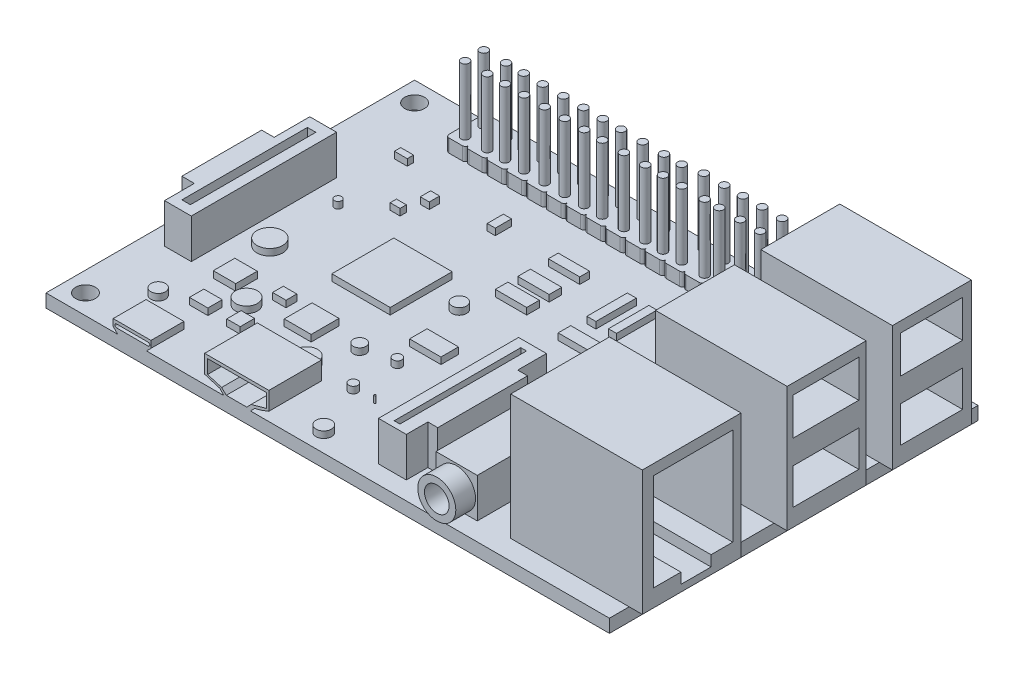
SolidWorks part; units mm, degrees
ref_plane "前视基准面" through (0, 0, 0) normal (0, 0, 1) x (1, 0, 0)
ref_plane "上视基准面" through (0, 0, 0) normal (0, 1, 0) x (1, 0, 0)
ref_plane "右视基准面" through (0, 0, 0) normal (1, 0, 0) x (0, 0, -1)
sketch "草图1" plane through (0, 0, 0) normal (0, 1, 0) x (1, 0, 0)
  line L1 (-42.8, -28) -> (42.8, -28)
  line L2 (-42.8, -28) -> (-42.8, 28)
  line L3 (-42.8, 28) -> (42.8, 28)
  line L4 (42.8, -28) -> (42.8, 28)
  line L5 (-42.8, -28) -> (42.8, 28) construction
  line L6 (-42.8, 28) -> (42.8, -28) construction
  circle A0 centre (-39.8, 25) radius 1.5
  circle A3 centre (-39.8, -25) radius 1.5
  point P0 (0, 0)
  dimension "D3" = 3
  dimension "D4" = 3
  dimension "D1" = 85.6
  dimension "D2" = 56
  dimension "D10" = 3
extrude "凸台-拉伸1" add sketch "草图1" along normal blind 2
sketch "草图2" plane through (0, 2, 0) normal (0, 1, 0) x (1, 0, 0)
  line L0 (42.8, -28) -> (42.8, 28) construction
  line L1 (24.8, -25) -> (44.8, -25)
  line L2 (24.8, -25) -> (24.8, -10)
  line L3 (24.8, -10) -> (44.8, -10)
  line L4 (44.8, -25) -> (44.8, -10)
  line L5 (24.8, -3) -> (44.8, -3)
  line L6 (24.8, -3) -> (24.8, 9)
  line L7 (24.8, 9) -> (44.8, 9)
  line L8 (44.8, -3) -> (44.8, 9)
  line L9 (24.8, 13) -> (44.8, 13)
  line L10 (24.8, 13) -> (24.8, 25)
  line L11 (24.8, 25) -> (44.8, 25)
  line L12 (44.8, 13) -> (44.8, 25)
  line L13 (-42.8, -28) -> (42.8, -28) construction
  line L14 (42.8, 28) -> (-42.8, 28) construction
  point P16 (34.8, 25)
  dimension "D1" = 12
  dimension "D2" = 12
  dimension "D3" = 15
  dimension "D4" = 20
  dimension "D5" = 2
  dimension "D6" = 2
  dimension "D7" = 20
  dimension "D8" = 20
  dimension "D9" = 2
  dimension "D10" = 3
  dimension "D11" = 3
  dimension "D12" = 4
extrude "凸台-拉伸2" add sketch "草图2" along normal blind 19
sketch "草图3" plane through (44.8, 0, 0) normal (1, 0, 0) x (0, 0, -1)
  line L0 (-23.3228, 19.3977) -> (-23.3228, 4.6356)
  line L1 (-23.3228, 4.6356) -> (-19.1436, 4.6356)
  line L2 (-19.1436, 4.6356) -> (-19.1436, 3.0178)
  line L3 (-19.1436, 3.0178) -> (-14.5599, 3.0178)
  line L4 (-14.5599, 3.0178) -> (-14.5599, 4.6356)
  line L5 (-14.5599, 4.6356) -> (-11.257, 4.6356)
  line L6 (-11.257, 4.6356) -> (-11.257, 19.3977)
  line L7 (-11.257, 19.3977) -> (-23.3228, 19.3977)
  line L9 (-2.0896, 19.3977) -> (7.8866, 19.3977)
  line L10 (-2.0896, 19.3977) -> (-2.0896, 13.7355)
  line L11 (-2.0896, 13.7355) -> (7.8866, 13.7355)
  line L12 (7.8866, 19.3977) -> (7.8866, 13.7355)
  line L13 (-2.0896, 10.0956) -> (7.8866, 10.0956)
  line L14 (-2.0896, 10.0956) -> (-2.0896, 4.6356)
  line L15 (-2.0896, 4.6356) -> (7.8866, 4.6356)
  line L16 (7.8866, 10.0956) -> (7.8866, 4.6356)
  line L17 (14.2229, 19.3977) -> (23.6598, 19.3977)
  line L18 (14.2229, 19.3977) -> (14.2229, 13.7355)
  line L19 (14.2229, 13.7355) -> (23.6598, 13.7355)
  line L20 (23.6598, 19.3977) -> (23.6598, 13.7355)
  line L21 (14.2229, 10.0956) -> (23.6598, 10.0956)
  line L22 (14.2229, 10.0956) -> (14.2229, 4.6356)
  line L23 (14.2229, 4.6356) -> (23.6598, 4.6356)
  line L24 (23.6598, 10.0956) -> (23.6598, 4.6356)
extrude "切除-拉伸1" cut sketch "草图3" against normal blind 18
sketch "草图4" plane through (0, 2, 0) normal (0, 1, 0) x (1, 0, 0)
  line L0 (4.9572, -25.2445) -> (4.9572, -3.9572)
  line L1 (13.6905, -25.2445) -> (19.9675, -25.2445)
  line L2 (13.6905, -25.2445) -> (13.6905, -10.2342)
  line L3 (13.6905, -10.2342) -> (19.9675, -10.2342)
  line L4 (19.9675, -25.2445) -> (19.9675, -10.2342)
  line L5 (4.9572, -3.9572) -> (9.1874, -3.9572)
  line L6 (9.1874, -3.9572) -> (9.1874, -8.3239)
  line L7 (9.1874, -8.3239) -> (10.6884, -8.3239)
  line L8 (10.6884, -8.3239) -> (10.6884, -21.9695)
  line L9 (10.6884, -21.9695) -> (9.1874, -21.9695)
  line L10 (9.1874, -21.9695) -> (9.1874, -25.2445)
  line L11 (9.1874, -25.2445) -> (4.9572, -25.2445)
  line L12 (-35.88, -12.8475) -> (-35.88, 9.2174)
  line L13 (6.4698, -24.3711) -> (7.3443, -24.3711)
  line L14 (6.4698, -24.3711) -> (6.4698, -5.1307)
  line L15 (6.4698, -5.1307) -> (7.3443, -5.1307)
  line L16 (7.3443, -24.3711) -> (7.3443, -5.1307)
  line L17 (-35.88, 9.2174) -> (-39.941, 9.2174)
  line L18 (-39.941, 9.2174) -> (-39.941, 3.8027)
  line L19 (-39.941, 3.8027) -> (-41.8361, 3.8027)
  line L20 (-41.8361, 3.8027) -> (-41.8361, -8.3239)
  line L21 (-41.8361, -8.3239) -> (-39.941, -8.3239)
  line L22 (-39.941, -8.3239) -> (-39.941, -12.8475)
  line L23 (-39.941, -12.8475) -> (-35.88, -12.8475)
  line L25 (-38.7205, -11.4317) -> (-37.4349, -11.4317)
  line L26 (-38.7205, -11.4317) -> (-38.7205, 7.6329)
  line L27 (-38.7205, 7.6329) -> (-37.4349, 7.6329)
  line L28 (-37.4349, -11.4317) -> (-37.4349, 7.6329)
extrude "凸台-拉伸3" add sketch "草图4" along normal blind 6
sketch "草图5" plane through (0, 0, 25.2445) normal (0, 0, 1) x (1, 0, 0)
  circle A0 centre (16.8166, 4.8134) radius 2.8909
  circle A1 centre (16.8166, 4.8134) radius 1.8682
extrude "凸台-拉伸4" add sketch "草图5" along normal blind 3
sketch "草图6" plane through (0, 0, 28) normal (0, 0, 1) x (1, 0, 0)
  line L0 (-31.9132, 2) -> (-32.596, 2.6828)
  line L1 (-42.8, 2) -> (16.1517, 2) construction
  line L2 (-32.596, 2.6828) -> (-32.596, 3.7273)
  line L3 (-32.596, 3.7273) -> (-26.8487, 3.7273)
  line L4 (-26.8487, 3.7273) -> (-26.8487, 2.6828)
  line L5 (-26.8487, 2.6828) -> (-27.5315, 2)
  line L6 (-27.5315, 2) -> (-31.9132, 2)
  line L7 (-32.093, 3.0167) -> (-27.2853, 3.0167) construction
  line L8 (-32.093, 3.2738) -> (-27.2853, 3.2738)
  line L9 (-32.093, 2.7595) -> (-27.2853, 2.7595)
  arc A0 (-32.093, 3.2738) -> (-32.093, 2.7595) centre (-32.093, 3.0167) ccw
  arc A1 (-27.2853, 2.7595) -> (-27.2853, 3.2738) centre (-27.2853, 3.0167) ccw
  point P10 (-29.6892, 3.0167)
extrude "凸台-拉伸5" add sketch "草图6" against normal blind 5
sketch "草图7" plane through (0, 0, 28) normal (0, 0, 1) x (1, 0, 0)
  line L0 (-18.6957, 6.1071) -> (-18.6957, 3.3548)
  line L1 (-18.6957, 3.3548) -> (-17.2094, 2.9048)
  line L2 (-17.2094, 2.9048) -> (-16.3918, 2.6574)
  line L3 (-16.3918, 2.6574) -> (-15.7754, 2)
  line L4 (-27.5315, 2) -> (16.1517, 2) construction
  line L5 (-15.7754, 2) -> (-11.7399, 2)
  line L6 (-11.7399, 2) -> (-11.0825, 2.6574)
  line L7 (-11.0825, 2.6574) -> (-10.1235, 2.9048)
  line L8 (-10.1235, 2.9048) -> (-8.9408, 3.3548)
  line L9 (-8.9408, 3.3548) -> (-8.9408, 6.1071)
  line L10 (-8.9408, 6.1071) -> (-18.6957, 6.1071)
  line L11 (-18.2447, 5.6338) -> (-18.2447, 3.5444)
  line L12 (-18.2447, 3.5444) -> (-16.1159, 2.9048)
  line L13 (-16.1159, 2.9048) -> (-15.4063, 2.2237)
  line L14 (-15.4063, 2.2237) -> (-12.2918, 2.2237)
  line L15 (-12.2918, 2.2237) -> (-11.638, 2.9048)
  line L16 (-11.638, 2.9048) -> (-9.3153, 3.5444)
  line L17 (-9.3153, 3.5444) -> (-9.3153, 5.6338)
  line L18 (-9.3153, 5.6338) -> (-18.2447, 5.6338)
extrude "凸台-拉伸6" add sketch "草图7" against normal blind 8
sketch "草图8" plane through (0, 2, 0) normal (0, 1, 0) x (1, 0, 0)
  line L0 (-24.5582, 21) -> (-22.5582, 21)
  line L1 (-30.5582, 21) -> (-28.5582, 21)
  line L2 (-31.0582, 21.5) -> (-31.0582, 23.5)
  line L3 (-30.5582, 24) -> (-28.5582, 24)
  line L4 (-28.0582, 21.5) -> (-28.0582, 23.5)
  line L5 (-30.5582, 24) -> (-28.5582, 24)
  line L6 (-31.0582, 24.5) -> (-31.0582, 26.5)
  line L7 (-30.5582, 27) -> (-28.5582, 27)
  line L8 (-28.0582, 24.5) -> (-28.0582, 26.5)
  line L9 (-25.0582, 21.5) -> (-25.0582, 23.5)
  line L10 (-24.5582, 24) -> (-22.5582, 24)
  line L11 (-22.0582, 21.5) -> (-22.0582, 23.5)
  line L12 (-24.5582, 24) -> (-22.5582, 24)
  line L13 (-25.0582, 24.5) -> (-25.0582, 26.5)
  line L14 (-24.5582, 27) -> (-22.5582, 27)
  line L15 (-22.0582, 24.5) -> (-22.0582, 26.5)
  line L16 (-27.5582, 21) -> (-25.5582, 21)
  line L17 (-28.0582, 21.5) -> (-28.0582, 23.5)
  line L18 (-27.5582, 24) -> (-25.5582, 24)
  line L19 (-25.0582, 21.5) -> (-25.0582, 23.5)
  line L20 (-27.5582, 24) -> (-25.5582, 24)
  line L21 (-28.0582, 24.5) -> (-28.0582, 26.5)
  line L22 (-27.5582, 27) -> (-25.5582, 27)
  line L23 (-25.0582, 24.5) -> (-25.0582, 26.5)
  line L24 (-21.5582, 21) -> (-19.5582, 21)
  line L25 (-22.0582, 21.5) -> (-22.0582, 23.5)
  line L26 (-21.5582, 24) -> (-19.5582, 24)
  line L27 (-19.0582, 21.5) -> (-19.0582, 23.5)
  line L28 (-21.5582, 24) -> (-19.5582, 24)
  line L29 (-22.0582, 24.5) -> (-22.0582, 26.5)
  line L30 (-21.5582, 27) -> (-19.5582, 27)
  line L31 (-19.0582, 24.5) -> (-19.0582, 26.5)
  line L32 (-18.5582, 21) -> (-16.5582, 21)
  line L33 (-19.0582, 21.5) -> (-19.0582, 23.5)
  line L34 (-18.5582, 24) -> (-16.5582, 24)
  line L35 (-16.0582, 21.5) -> (-16.0582, 23.5)
  line L36 (-18.5582, 24) -> (-16.5582, 24)
  line L37 (-19.0582, 24.5) -> (-19.0582, 26.5)
  line L38 (-18.5582, 27) -> (-16.5582, 27)
  line L39 (-16.0582, 24.5) -> (-16.0582, 26.5)
  line L40 (-15.5582, 21) -> (-13.5582, 21)
  line L41 (-16.0582, 21.5) -> (-16.0582, 23.5)
  line L42 (-15.5582, 24) -> (-13.5582, 24)
  line L43 (-13.0582, 21.5) -> (-13.0582, 23.5)
  line L44 (-15.5582, 24) -> (-13.5582, 24)
  line L45 (-16.0582, 24.5) -> (-16.0582, 26.5)
  line L46 (-15.5582, 27) -> (-13.5582, 27)
  line L47 (-13.0582, 24.5) -> (-13.0582, 26.5)
  line L48 (-12.5582, 21) -> (-10.5582, 21)
  line L49 (-13.0582, 21.5) -> (-13.0582, 23.5)
  line L50 (-12.5582, 24) -> (-10.5582, 24)
  line L51 (-10.0582, 21.5) -> (-10.0582, 23.5)
  line L52 (-12.5582, 24) -> (-10.5582, 24)
  line L53 (-13.0582, 24.5) -> (-13.0582, 26.5)
  line L54 (-12.5582, 27) -> (-10.5582, 27)
  line L55 (-10.0582, 24.5) -> (-10.0582, 26.5)
  line L56 (-9.5582, 21) -> (-7.5582, 21)
  line L57 (-10.0582, 21.5) -> (-10.0582, 23.5)
  line L58 (-9.5582, 24) -> (-7.5582, 24)
  line L59 (-7.0582, 21.5) -> (-7.0582, 23.5)
  line L60 (-9.5582, 24) -> (-7.5582, 24)
  line L61 (-10.0582, 24.5) -> (-10.0582, 26.5)
  line L62 (-9.5582, 27) -> (-7.5582, 27)
  line L63 (-7.0582, 24.5) -> (-7.0582, 26.5)
  line L64 (42.8, 28) -> (-42.8, 28) construction
  line L65 (-0.5582, 21) -> (1.4418, 21)
  line L66 (-6.5582, 21) -> (-4.5582, 21)
  line L67 (-7.0582, 21.5) -> (-7.0582, 23.5)
  line L68 (-6.5582, 24) -> (-4.5582, 24)
  line L69 (-4.0582, 21.5) -> (-4.0582, 23.5)
  line L70 (-6.5582, 24) -> (-4.5582, 24)
  line L71 (-7.0582, 24.5) -> (-7.0582, 26.5)
  line L72 (-6.5582, 27) -> (-4.5582, 27)
  line L73 (-4.0582, 24.5) -> (-4.0582, 26.5)
  line L74 (-1.0582, 21.5) -> (-1.0582, 23.5)
  line L75 (-0.5582, 24) -> (1.4418, 24)
  line L76 (1.9418, 21.5) -> (1.9418, 23.5)
  line L77 (-0.5582, 24) -> (1.4418, 24)
  line L78 (-1.0582, 24.5) -> (-1.0582, 26.5)
  line L79 (-0.5582, 27) -> (1.4418, 27)
  line L80 (1.9418, 24.5) -> (1.9418, 26.5)
  line L81 (-3.5582, 21) -> (-1.5582, 21)
  line L82 (-4.0582, 21.5) -> (-4.0582, 23.5)
  line L83 (-3.5582, 24) -> (-1.5582, 24)
  line L84 (-1.0582, 21.5) -> (-1.0582, 23.5)
  line L85 (-3.5582, 24) -> (-1.5582, 24)
  line L86 (-4.0582, 24.5) -> (-4.0582, 26.5)
  line L87 (-3.5582, 27) -> (-1.5582, 27)
  line L88 (-1.0582, 24.5) -> (-1.0582, 26.5)
  line L89 (2.4418, 21) -> (4.4418, 21)
  line L90 (1.9418, 21.5) -> (1.9418, 23.5)
  line L91 (2.4418, 24) -> (4.4418, 24)
  line L92 (4.9418, 21.5) -> (4.9418, 23.5)
  line L93 (2.4418, 24) -> (4.4418, 24)
  line L94 (1.9418, 24.5) -> (1.9418, 26.5)
  line L95 (2.4418, 27) -> (4.4418, 27)
  line L96 (4.9418, 24.5) -> (4.9418, 26.5)
  line L97 (5.4418, 21) -> (7.4418, 21)
  line L98 (4.9418, 21.5) -> (4.9418, 23.5)
  line L99 (5.4418, 24) -> (7.4418, 24)
  line L100 (7.9418, 21.5) -> (7.9418, 23.5)
  line L101 (5.4418, 24) -> (7.4418, 24)
  line L102 (4.9418, 24.5) -> (4.9418, 26.5)
  line L103 (5.4418, 27) -> (7.4418, 27)
  line L104 (7.9418, 24.5) -> (7.9418, 26.5)
  line L105 (8.4418, 21) -> (10.4418, 21)
  line L106 (7.9418, 21.5) -> (7.9418, 23.5)
  line L107 (8.4418, 24) -> (10.4418, 24)
  line L108 (10.9418, 21.5) -> (10.9418, 23.5)
  line L109 (8.4418, 24) -> (10.4418, 24)
  line L110 (7.9418, 24.5) -> (7.9418, 26.5)
  line L111 (8.4418, 27) -> (10.4418, 27)
  line L112 (10.9418, 24.5) -> (10.9418, 26.5)
  line L113 (11.4418, 21) -> (13.4418, 21)
  line L114 (10.9418, 21.5) -> (10.9418, 23.5)
  line L115 (11.4418, 24) -> (13.4418, 24)
  line L116 (13.9418, 21.5) -> (13.9418, 23.5)
  line L117 (11.4418, 24) -> (13.4418, 24)
  line L118 (10.9418, 24.5) -> (10.9418, 26.5)
  line L119 (11.4418, 27) -> (13.4418, 27)
  line L120 (13.9418, 24.5) -> (13.9418, 26.5)
  line L121 (14.4418, 21) -> (16.4418, 21)
  line L122 (13.9418, 21.5) -> (13.9418, 23.5)
  line L123 (14.4418, 24) -> (16.4418, 24)
  line L124 (16.9418, 21.5) -> (16.9418, 23.5)
  line L125 (14.4418, 24) -> (16.4418, 24)
  line L126 (13.9418, 24.5) -> (13.9418, 26.5)
  line L127 (14.4418, 27) -> (16.4418, 27)
  line L128 (16.9418, 24.5) -> (16.9418, 26.5)
  arc A0 (-28.5582, 27) -> (-28.0582, 26.5) centre (-28.5582, 26.5) cw
  arc A1 (-28.5582, 24) -> (-28.0582, 24.5) centre (-28.5582, 24.5) ccw
  arc A2 (-31.0582, 26.5) -> (-30.5582, 27) centre (-30.5582, 26.5) cw
  arc A3 (-30.5582, 24) -> (-31.0582, 24.5) centre (-30.5582, 24.5) cw
  arc A4 (-31.0582, 23.5) -> (-30.5582, 24) centre (-30.5582, 23.5) cw
  arc A5 (-28.5582, 24) -> (-28.0582, 23.5) centre (-28.5582, 23.5) cw
  arc A6 (-28.5582, 21) -> (-28.0582, 21.5) centre (-28.5582, 21.5) ccw
  arc A7 (-30.5582, 21) -> (-31.0582, 21.5) centre (-30.5582, 21.5) cw
  arc A8 (-22.5582, 27) -> (-22.0582, 26.5) centre (-22.5582, 26.5) cw
  arc A9 (-22.5582, 24) -> (-22.0582, 24.5) centre (-22.5582, 24.5) ccw
  arc A10 (-25.0582, 26.5) -> (-24.5582, 27) centre (-24.5582, 26.5) cw
  arc A11 (-24.5582, 24) -> (-25.0582, 24.5) centre (-24.5582, 24.5) cw
  arc A12 (-25.0582, 23.5) -> (-24.5582, 24) centre (-24.5582, 23.5) cw
  arc A13 (-22.5582, 24) -> (-22.0582, 23.5) centre (-22.5582, 23.5) cw
  arc A14 (-22.5582, 21) -> (-22.0582, 21.5) centre (-22.5582, 21.5) ccw
  arc A15 (-24.5582, 21) -> (-25.0582, 21.5) centre (-24.5582, 21.5) cw
  arc A16 (-25.5582, 27) -> (-25.0582, 26.5) centre (-25.5582, 26.5) cw
  arc A17 (-25.5582, 24) -> (-25.0582, 24.5) centre (-25.5582, 24.5) ccw
  arc A18 (-28.0582, 26.5) -> (-27.5582, 27) centre (-27.5582, 26.5) cw
  arc A19 (-27.5582, 24) -> (-28.0582, 24.5) centre (-27.5582, 24.5) cw
  arc A20 (-28.0582, 23.5) -> (-27.5582, 24) centre (-27.5582, 23.5) cw
  arc A21 (-25.5582, 24) -> (-25.0582, 23.5) centre (-25.5582, 23.5) cw
  arc A22 (-25.5582, 21) -> (-25.0582, 21.5) centre (-25.5582, 21.5) ccw
  arc A23 (-27.5582, 21) -> (-28.0582, 21.5) centre (-27.5582, 21.5) cw
  arc A24 (-19.5582, 27) -> (-19.0582, 26.5) centre (-19.5582, 26.5) cw
  arc A25 (-19.5582, 24) -> (-19.0582, 24.5) centre (-19.5582, 24.5) ccw
  arc A26 (-22.0582, 26.5) -> (-21.5582, 27) centre (-21.5582, 26.5) cw
  arc A27 (-21.5582, 24) -> (-22.0582, 24.5) centre (-21.5582, 24.5) cw
  arc A28 (-22.0582, 23.5) -> (-21.5582, 24) centre (-21.5582, 23.5) cw
  arc A29 (-19.5582, 24) -> (-19.0582, 23.5) centre (-19.5582, 23.5) cw
  arc A30 (-19.5582, 21) -> (-19.0582, 21.5) centre (-19.5582, 21.5) ccw
  arc A31 (-21.5582, 21) -> (-22.0582, 21.5) centre (-21.5582, 21.5) cw
  arc A32 (-16.5582, 27) -> (-16.0582, 26.5) centre (-16.5582, 26.5) cw
  arc A33 (-16.5582, 24) -> (-16.0582, 24.5) centre (-16.5582, 24.5) ccw
  arc A34 (-19.0582, 26.5) -> (-18.5582, 27) centre (-18.5582, 26.5) cw
  arc A35 (-18.5582, 24) -> (-19.0582, 24.5) centre (-18.5582, 24.5) cw
  arc A36 (-19.0582, 23.5) -> (-18.5582, 24) centre (-18.5582, 23.5) cw
  arc A37 (-16.5582, 24) -> (-16.0582, 23.5) centre (-16.5582, 23.5) cw
  arc A38 (-16.5582, 21) -> (-16.0582, 21.5) centre (-16.5582, 21.5) ccw
  arc A39 (-18.5582, 21) -> (-19.0582, 21.5) centre (-18.5582, 21.5) cw
  arc A40 (-13.5582, 27) -> (-13.0582, 26.5) centre (-13.5582, 26.5) cw
  arc A41 (-13.5582, 24) -> (-13.0582, 24.5) centre (-13.5582, 24.5) ccw
  arc A42 (-16.0582, 26.5) -> (-15.5582, 27) centre (-15.5582, 26.5) cw
  arc A43 (-15.5582, 24) -> (-16.0582, 24.5) centre (-15.5582, 24.5) cw
  arc A44 (-16.0582, 23.5) -> (-15.5582, 24) centre (-15.5582, 23.5) cw
  arc A45 (-13.5582, 24) -> (-13.0582, 23.5) centre (-13.5582, 23.5) cw
  arc A46 (-13.5582, 21) -> (-13.0582, 21.5) centre (-13.5582, 21.5) ccw
  arc A47 (-15.5582, 21) -> (-16.0582, 21.5) centre (-15.5582, 21.5) cw
  arc A48 (-10.5582, 27) -> (-10.0582, 26.5) centre (-10.5582, 26.5) cw
  arc A49 (-10.5582, 24) -> (-10.0582, 24.5) centre (-10.5582, 24.5) ccw
  arc A50 (-13.0582, 26.5) -> (-12.5582, 27) centre (-12.5582, 26.5) cw
  arc A51 (-12.5582, 24) -> (-13.0582, 24.5) centre (-12.5582, 24.5) cw
  arc A52 (-13.0582, 23.5) -> (-12.5582, 24) centre (-12.5582, 23.5) cw
  arc A53 (-10.5582, 24) -> (-10.0582, 23.5) centre (-10.5582, 23.5) cw
  arc A54 (-10.5582, 21) -> (-10.0582, 21.5) centre (-10.5582, 21.5) ccw
  arc A55 (-12.5582, 21) -> (-13.0582, 21.5) centre (-12.5582, 21.5) cw
  arc A56 (-7.5582, 27) -> (-7.0582, 26.5) centre (-7.5582, 26.5) cw
  arc A57 (-7.5582, 24) -> (-7.0582, 24.5) centre (-7.5582, 24.5) ccw
  arc A58 (-10.0582, 26.5) -> (-9.5582, 27) centre (-9.5582, 26.5) cw
  arc A59 (-9.5582, 24) -> (-10.0582, 24.5) centre (-9.5582, 24.5) cw
  arc A60 (-10.0582, 23.5) -> (-9.5582, 24) centre (-9.5582, 23.5) cw
  arc A61 (-7.5582, 24) -> (-7.0582, 23.5) centre (-7.5582, 23.5) cw
  arc A62 (-7.5582, 21) -> (-7.0582, 21.5) centre (-7.5582, 21.5) ccw
  arc A63 (-9.5582, 21) -> (-10.0582, 21.5) centre (-9.5582, 21.5) cw
  arc A64 (-4.5582, 27) -> (-4.0582, 26.5) centre (-4.5582, 26.5) cw
  arc A65 (-4.5582, 24) -> (-4.0582, 24.5) centre (-4.5582, 24.5) ccw
  arc A66 (-7.0582, 26.5) -> (-6.5582, 27) centre (-6.5582, 26.5) cw
  arc A67 (-6.5582, 24) -> (-7.0582, 24.5) centre (-6.5582, 24.5) cw
  arc A68 (-7.0582, 23.5) -> (-6.5582, 24) centre (-6.5582, 23.5) cw
  arc A69 (-4.5582, 24) -> (-4.0582, 23.5) centre (-4.5582, 23.5) cw
  arc A70 (-4.5582, 21) -> (-4.0582, 21.5) centre (-4.5582, 21.5) ccw
  arc A71 (-6.5582, 21) -> (-7.0582, 21.5) centre (-6.5582, 21.5) cw
  arc A72 (1.4418, 27) -> (1.9418, 26.5) centre (1.4418, 26.5) cw
  arc A73 (1.4418, 24) -> (1.9418, 24.5) centre (1.4418, 24.5) ccw
  arc A74 (-1.0582, 26.5) -> (-0.5582, 27) centre (-0.5582, 26.5) cw
  arc A75 (-0.5582, 24) -> (-1.0582, 24.5) centre (-0.5582, 24.5) cw
  arc A76 (-1.0582, 23.5) -> (-0.5582, 24) centre (-0.5582, 23.5) cw
  arc A77 (1.4418, 24) -> (1.9418, 23.5) centre (1.4418, 23.5) cw
  arc A78 (1.4418, 21) -> (1.9418, 21.5) centre (1.4418, 21.5) ccw
  arc A79 (-0.5582, 21) -> (-1.0582, 21.5) centre (-0.5582, 21.5) cw
  arc A80 (-1.5582, 27) -> (-1.0582, 26.5) centre (-1.5582, 26.5) cw
  arc A81 (-1.5582, 24) -> (-1.0582, 24.5) centre (-1.5582, 24.5) ccw
  arc A82 (-4.0582, 26.5) -> (-3.5582, 27) centre (-3.5582, 26.5) cw
  arc A83 (-3.5582, 24) -> (-4.0582, 24.5) centre (-3.5582, 24.5) cw
  arc A84 (-4.0582, 23.5) -> (-3.5582, 24) centre (-3.5582, 23.5) cw
  arc A85 (-1.5582, 24) -> (-1.0582, 23.5) centre (-1.5582, 23.5) cw
  arc A86 (-1.5582, 21) -> (-1.0582, 21.5) centre (-1.5582, 21.5) ccw
  arc A87 (-3.5582, 21) -> (-4.0582, 21.5) centre (-3.5582, 21.5) cw
  arc A88 (4.4418, 27) -> (4.9418, 26.5) centre (4.4418, 26.5) cw
  arc A89 (4.4418, 24) -> (4.9418, 24.5) centre (4.4418, 24.5) ccw
  arc A90 (1.9418, 26.5) -> (2.4418, 27) centre (2.4418, 26.5) cw
  arc A91 (2.4418, 24) -> (1.9418, 24.5) centre (2.4418, 24.5) cw
  arc A92 (1.9418, 23.5) -> (2.4418, 24) centre (2.4418, 23.5) cw
  arc A93 (4.4418, 24) -> (4.9418, 23.5) centre (4.4418, 23.5) cw
  arc A94 (4.4418, 21) -> (4.9418, 21.5) centre (4.4418, 21.5) ccw
  arc A95 (2.4418, 21) -> (1.9418, 21.5) centre (2.4418, 21.5) cw
  arc A96 (7.4418, 27) -> (7.9418, 26.5) centre (7.4418, 26.5) cw
  arc A97 (7.4418, 24) -> (7.9418, 24.5) centre (7.4418, 24.5) ccw
  arc A98 (4.9418, 26.5) -> (5.4418, 27) centre (5.4418, 26.5) cw
  arc A99 (5.4418, 24) -> (4.9418, 24.5) centre (5.4418, 24.5) cw
  arc A100 (4.9418, 23.5) -> (5.4418, 24) centre (5.4418, 23.5) cw
  arc A101 (7.4418, 24) -> (7.9418, 23.5) centre (7.4418, 23.5) cw
  arc A102 (7.4418, 21) -> (7.9418, 21.5) centre (7.4418, 21.5) ccw
  arc A103 (5.4418, 21) -> (4.9418, 21.5) centre (5.4418, 21.5) cw
  arc A104 (10.4418, 27) -> (10.9418, 26.5) centre (10.4418, 26.5) cw
  arc A105 (10.4418, 24) -> (10.9418, 24.5) centre (10.4418, 24.5) ccw
  arc A106 (7.9418, 26.5) -> (8.4418, 27) centre (8.4418, 26.5) cw
  arc A107 (8.4418, 24) -> (7.9418, 24.5) centre (8.4418, 24.5) cw
  arc A108 (7.9418, 23.5) -> (8.4418, 24) centre (8.4418, 23.5) cw
  arc A109 (10.4418, 24) -> (10.9418, 23.5) centre (10.4418, 23.5) cw
  arc A110 (10.4418, 21) -> (10.9418, 21.5) centre (10.4418, 21.5) ccw
  arc A111 (8.4418, 21) -> (7.9418, 21.5) centre (8.4418, 21.5) cw
  arc A112 (13.4418, 27) -> (13.9418, 26.5) centre (13.4418, 26.5) cw
  arc A113 (13.4418, 24) -> (13.9418, 24.5) centre (13.4418, 24.5) ccw
  arc A114 (10.9418, 26.5) -> (11.4418, 27) centre (11.4418, 26.5) cw
  arc A115 (11.4418, 24) -> (10.9418, 24.5) centre (11.4418, 24.5) cw
  arc A116 (10.9418, 23.5) -> (11.4418, 24) centre (11.4418, 23.5) cw
  arc A117 (13.4418, 24) -> (13.9418, 23.5) centre (13.4418, 23.5) cw
  arc A118 (13.4418, 21) -> (13.9418, 21.5) centre (13.4418, 21.5) ccw
  arc A119 (11.4418, 21) -> (10.9418, 21.5) centre (11.4418, 21.5) cw
  arc A120 (16.4418, 27) -> (16.9418, 26.5) centre (16.4418, 26.5) cw
  arc A121 (16.4418, 24) -> (16.9418, 24.5) centre (16.4418, 24.5) ccw
  arc A122 (13.9418, 26.5) -> (14.4418, 27) centre (14.4418, 26.5) cw
  arc A123 (14.4418, 24) -> (13.9418, 24.5) centre (14.4418, 24.5) cw
  arc A124 (13.9418, 23.5) -> (14.4418, 24) centre (14.4418, 23.5) cw
  arc A125 (16.4418, 24) -> (16.9418, 23.5) centre (16.4418, 23.5) cw
  arc A126 (16.4418, 21) -> (16.9418, 21.5) centre (16.4418, 21.5) ccw
  arc A127 (14.4418, 21) -> (13.9418, 21.5) centre (14.4418, 21.5) cw
  dimension "D1" = 0.5
  dimension "D6" = 0.5
  dimension "D11" = 0.5
  dimension "D16" = 0.5
  dimension "D21" = 0.5
  dimension "D26" = 0.5
  dimension "D31" = 0.5
  dimension "D36" = 0.5
  dimension "D42" = 0.5
  dimension "D47" = 0.5
  dimension "D52" = 0.5
  dimension "D57" = 0.5
  dimension "D62" = 0.5
  dimension "D67" = 0.5
  dimension "D72" = 0.5
  dimension "D77" = 0.5
  dimension "D2" = 2
  dimension "D3" = 2
  dimension "D4" = 2
  dimension "D5" = 2
  dimension "D7" = 2
  dimension "D8" = 2
  dimension "D9" = 2
  dimension "D10" = 2
  dimension "D12" = 2
  dimension "D13" = 2
  dimension "D14" = 2
  dimension "D15" = 2
  dimension "D17" = 2
  dimension "D18" = 2
  dimension "D19" = 2
  dimension "D20" = 2
  dimension "D22" = 2
  dimension "D23" = 2
  dimension "D24" = 2
  dimension "D25" = 2
  dimension "D27" = 2
  dimension "D28" = 2
  dimension "D29" = 2
  dimension "D30" = 2
  dimension "D32" = 2
  dimension "D33" = 2
  dimension "D34" = 2
  dimension "D35" = 2
  dimension "D37" = 2
  dimension "D38" = 2
  dimension "D39" = 2
  dimension "D40" = 2
  dimension "D41" = 4
  dimension "D43" = 2
  dimension "D44" = 2
  dimension "D45" = 2
  dimension "D46" = 2
  dimension "D48" = 2
  dimension "D49" = 2
  dimension "D50" = 2
  dimension "D51" = 2
  dimension "D53" = 2
  dimension "D54" = 2
  dimension "D55" = 2
  dimension "D56" = 2
  dimension "D58" = 2
  dimension "D59" = 2
  dimension "D60" = 2
  dimension "D61" = 2
  dimension "D63" = 2
  dimension "D64" = 2
  dimension "D65" = 2
  dimension "D66" = 2
  dimension "D68" = 2
  dimension "D69" = 2
  dimension "D70" = 2
  dimension "D71" = 2
  dimension "D73" = 2
  dimension "D74" = 2
  dimension "D75" = 2
  dimension "D76" = 2
  dimension "D78" = 2
  dimension "D79" = 2
  dimension "D80" = 2
  dimension "D81" = 2
  dimension "D82" = 4
extrude "凸台-拉伸7" add sketch "草图8" along normal blind 2 contours A127 L121 A126 L124 A125 L123 A124 L116 | A123 L123 A121 L128 A120 L127 A122 L120 | A119 L113 A118 L116 A117 L115 A116 L108 | A115 L115 A113 L120 A112 L119 A114 L112 | A111 L105 A110 L108 A109 L107 A108 L100 | A107 L107 A105 L112 A104 L111 A106 L104 | A103 L97 A102 L100 A101 L99 A100 L92 | A99 L99 A97 L104 A96 L103 A98 L96 | A91 L91 A89 L96 A88 L95 A90 L80 | A95 L89 A94 L92 A93 L91 A92 L76 | A79 L65 A78 L76 A77 L75 A76 L74 | A75 L75 A73 L80 A72 L79 A74 L78 | A83 L83 A81 L78 A80 L87 A82 L73 | A87 L81 A86 L74 A85 L83 A84 L69 | A71 L66 A70 L69 A69 L68 A68 L59 | A59 L58 A57 L63 A56 L62 A58 L55 | A63 L56 A62 L59 A61 L58 A60 L51 | A67 L68 A65 L73 A64 L72 A66 L63 | A51 L50 A49 L55 A48 L54 A50 L47 | A55 L48 A54 L51 A53 L50 A52 L43 | A47 L40 A46 L43 A45 L42 A44 L35 | A43 L42 A41 L47 A40 L46 A42 L39 | A39 L32 A38 L35 A37 L34 A36 L27 | A35 L34 A33 L39 A32 L38 A34 L31 | A31 L24 A30 L27 A29 L26 A28 L11 | A27 L26 A25 L31 A24 L30 A26 L15 | A15 L0 A14 L11 A13 L10 A12 L9 | A11 L10 A9 L15 A8 L14 A10 L13 | A23 L16 A22 L9 A21 L18 A20 L4 | A19 L18 A17 L13 A16 L22 A18 L8 | A7 L1 A6 L4 A5 L3 A4 L2
sketch "草图9" plane through (0, 2, 0) normal (0, 1, 0) x (1, 0, 0)
  line L0 (0, -11.55) -> (0, 11.55) construction
  line L1 (-22.607, -4.7681) -> (-13.7373, -4.7681)
  line L2 (-22.607, -4.7681) -> (-22.607, 4.6474)
  line L3 (-22.607, 4.6474) -> (-13.7373, 4.6474)
  line L4 (-13.7373, -4.7681) -> (-13.7373, 4.6474)
  line L5 (14.0998, 4.6474) -> (20.9227, 4.6474)
  line L6 (14.0998, 4.6474) -> (14.0998, 15.1545)
  line L7 (14.0998, 15.1545) -> (20.9227, 15.1545)
  line L8 (20.9227, 4.6474) -> (20.9227, 15.1545)
  line L9 (-32.0225, -13.3649) -> (-28.6111, -13.3649)
  line L10 (-32.0225, -13.3649) -> (-32.0225, -10.0899)
  line L11 (-32.0225, -10.0899) -> (-28.6111, -10.0899)
  line L12 (-28.6111, -13.3649) -> (-28.6111, -10.0899)
  line L13 (-30.3168, -18.6867) -> (-27.5194, -18.6867)
  line L14 (-30.3168, -18.6867) -> (-30.3168, -16.5034)
  line L15 (-30.3168, -16.5034) -> (-27.5194, -16.5034)
  line L16 (-27.5194, -18.6867) -> (-27.5194, -16.5034)
  line L17 (-20.2872, -14.3201) -> (-16.1935, -14.3201)
  line L18 (-20.2872, -14.3201) -> (-20.2872, -10.0899)
  line L19 (-20.2872, -10.0899) -> (-16.1935, -10.0899)
  line L20 (-16.1935, -14.3201) -> (-16.1935, -10.0899)
  line L21 (-24.6538, -18.6867) -> (-22.607, -18.6867)
  line L22 (-24.6538, -18.6867) -> (-24.6538, -16.5034)
  line L23 (-24.6538, -16.5034) -> (-22.607, -16.5034)
  line L24 (-22.607, -18.6867) -> (-22.607, -16.5034)
  line L25 (-24.6538, -11.7274) -> (-22.607, -11.7274)
  line L26 (-24.6538, -11.7274) -> (-24.6538, -10.0899)
  line L27 (-24.6538, -10.0899) -> (-22.607, -10.0899)
  line L28 (-22.607, -11.7274) -> (-22.607, -10.0899)
  line L29 (5.6395, 9.014) -> (6.8676, 9.014)
  line L30 (5.6395, 9.014) -> (5.6395, 15.1545)
  line L31 (5.6395, 15.1545) -> (6.8676, 15.1545)
  line L32 (6.8676, 9.014) -> (6.8676, 15.1545)
  line L33 (2.3646, 9.014) -> (3.7291, 9.014)
  line L34 (2.3646, 9.014) -> (2.3646, 15.1545)
  line L35 (2.3646, 15.1545) -> (3.7291, 15.1545)
  line L36 (3.7291, 9.014) -> (3.7291, 15.1545)
  line L37 (-8.1341, 13.6535) -> (-3.3666, 13.6535)
  line L38 (-8.1341, 13.6535) -> (-8.1341, 15.1545)
  line L39 (-8.1341, 15.1545) -> (-3.3666, 15.1545)
  line L40 (-3.3666, 13.6535) -> (-3.3666, 15.1545)
  line L41 (-8.1341, 9.014) -> (-3.3666, 9.014)
  line L42 (-8.1341, 9.014) -> (-8.1341, 10.9244)
  line L43 (-8.1341, 10.9244) -> (-3.3666, 10.9244)
  line L44 (-3.3666, 9.014) -> (-3.3666, 10.9244)
  line L45 (-8.1341, 5.6026) -> (-3.3666, 5.6026)
  line L46 (-8.1341, 5.6026) -> (-8.1341, 7.513)
  line L47 (-8.1341, 7.513) -> (-3.3666, 7.513)
  line L48 (-3.3666, 5.6026) -> (-3.3666, 7.513)
  line L49 (2.3646, 4.6474) -> (6.8676, 4.6474)
  line L50 (2.3646, 4.6474) -> (2.3646, 6.5578)
  line L51 (2.3646, 6.5578) -> (6.8676, 6.5578)
  line L52 (6.8676, 4.6474) -> (6.8676, 6.5578)
  line L53 (0, -18.6867) -> (2.3646, -18.6867)
  line L54 (0, -18.6867) -> (0, -13.3649)
  line L55 (0, -13.3649) -> (2.3646, -13.3649)
  line L56 (2.3646, -18.6867) -> (2.3646, -13.3649)
  line L58 (0, -10.0899) -> (2.3646, -10.0899)
  line L59 (0, -10.0899) -> (0, -4.7681)
  line L60 (0, -4.7681) -> (2.3646, -4.7681)
  line L61 (2.3646, -10.0899) -> (2.3646, -4.7681)
  line L62 (-8.1341, -7.429) -> (-3.3666, -7.429)
  line L63 (-8.1341, -7.429) -> (-8.1341, -4.7681)
  line L64 (-8.1341, -4.7681) -> (-3.3666, -4.7681)
  line L65 (-3.3666, -7.429) -> (-3.3666, -4.7681)
  line L66 (-27.5194, 9.014) -> (-26.0184, 9.014)
  line L67 (-27.5194, 9.014) -> (-27.5194, 9.9692)
  line L68 (-27.5194, 9.9692) -> (-26.0184, 9.9692)
  line L69 (-26.0184, 9.014) -> (-26.0184, 9.9692)
  line L70 (-26.0184, 12.0843) -> (-24.6538, 12.0843)
  line L71 (-26.0184, 12.0843) -> (-26.0184, 13.6535)
  line L72 (-26.0184, 13.6535) -> (-24.6538, 13.6535)
  line L73 (-24.6538, 12.0843) -> (-24.6538, 13.6535)
  line L78 (-33.9774, 16.1097) -> (-32.0225, 16.1097)
  line L79 (-33.9774, 16.1097) -> (-33.9774, 17.0649)
  line L80 (-33.9774, 17.0649) -> (-32.0225, 17.0649)
  line L81 (-32.0225, 16.1097) -> (-32.0225, 17.0649)
  line L82 (-17.4216, 13.6535) -> (-16.1935, 13.6535)
  line L83 (-17.4216, 13.6535) -> (-17.4216, 16.1097)
  line L84 (-17.4216, 16.1097) -> (-16.1935, 16.1097)
  line L85 (-16.1935, 13.6535) -> (-16.1935, 16.1097)
  circle A0 centre (-32.0225, 5.6026) radius 0.5458
  circle A1 centre (-32.0225, -4.7681) radius 1.955
  circle A2 centre (-33.9774, -19.7784) radius 1.0955
  circle A3 centre (-11.4175, -11.7274) radius 0.9552
  circle A4 centre (-26.0184, -14.3201) radius 1.6657
  circle A5 centre (-13.7373, -17.4586) radius 1.6657
  circle A6 centre (-6.6416, -17.4586) radius 0.6823
  circle A7 centre (-3.3666, -17.4586) radius 0.1365
  circle A8 centre (-3.3666, -25.2366) radius 1.1738
  circle A9 centre (-6.6416, -10.7722) radius 0.6823
  circle A10 centre (-9.2342, 1.236) radius 1.1001
extrude "凸台-拉伸9" add sketch "草图9" along normal blind 1
sketch "草图10" plane through (0, 4, 0) normal (0, 1, 0) x (1, 0, 0)
  circle A0 centre (-29.5127, 22.3878) radius 0.619
  circle A1 centre (-29.5127, 25.2288) radius 0.619
  circle A2 centre (-26.1342, 22.3878) radius 0.619
  circle A3 centre (-26.1342, 25.2288) radius 0.619
  circle A4 centre (-23.4468, 22.3878) radius 0.619
  circle A5 centre (-23.4468, 25.2288) radius 0.619
  circle A6 centre (-20.5582, 22.3878) radius 0.619
  circle A7 centre (-20.5582, 25.2288) radius 0.619
  circle A8 centre (-17.4327, 22.3878) radius 0.619
  circle A9 centre (-17.4327, 25.2288) radius 0.619
  circle A10 centre (-14.3724, 22.3878) radius 0.619
  circle A11 centre (-14.3724, 25.2288) radius 0.619
  circle A12 centre (-11.42, 22.3878) radius 0.619
  circle A13 centre (-11.42, 25.2288) radius 0.619
  circle A14 centre (-8.6664, 22.3878) radius 0.619
  circle A15 centre (-8.6664, 25.2288) radius 0.619
  circle A16 centre (-5.3793, 22.3878) radius 0.619
  circle A17 centre (-5.3793, 25.2288) radius 0.619
  circle A18 centre (-2.135, 22.3878) radius 0.619
  circle A19 centre (-2.135, 25.2288) radius 0.619
  circle A20 centre (0.5544, 22.3878) radius 0.619
  circle A21 centre (0.5544, 25.2288) radius 0.619
  circle A22 centre (3.411, 22.3878) radius 0.619
  circle A23 centre (3.411, 25.7297) radius 0.619
  circle A24 centre (6.8696, 22.3878) radius 0.619
  circle A25 centre (6.5322, 25.7297) radius 0.619
  circle A26 centre (9.1051, 22.3878) radius 0.619
  circle A27 centre (9.3582, 25.7297) radius 0.619
  circle A28 centre (12.2685, 22.3878) radius 0.619
  circle A29 centre (12.2685, 25.7297) radius 0.619
  circle A30 centre (15.3054, 22.3878) radius 0.619
  circle A31 centre (15.3054, 25.7297) radius 0.619
extrude "凸台-拉伸10" add sketch "草图10" along normal blind 10
